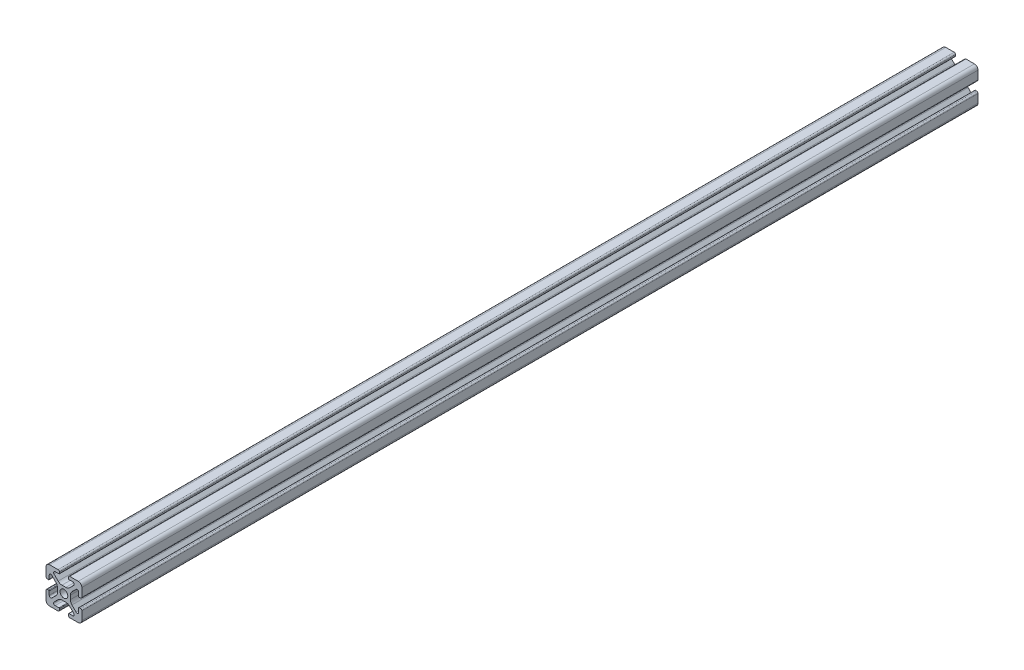
SolidWorks part; units mm, degrees
ref_plane "Front Plane" through (0, 0, 0) normal (0, 0, 1) x (1, 0, 0)
ref_plane "Top Plane" through (0, 0, 0) normal (0, 1, 0) x (1, 0, 0)
ref_plane "Right Plane" through (0, 0, 0) normal (1, 0, 0) x (0, 0, -1)
sketch "Sketch1" plane through (0, 0, 0) normal (0, 0, 1) x (1, 0, 0)
  line L0 (0, 10) -> (0, -10) construction
  line L1 (10, 0) -> (-10, 0) construction
  line L2 (-2.5, 10) -> (2.5, 10) construction
  line L3 (-5.75, 8.2) -> (5.75, 8.2) construction
  circle A0 centre (0, 0) radius 2.15 construction
  point P4 (0, 0)
  point P8 (0, 0)
  point P10 (0, 3.6)
  point P14 (0, 10)
  point P17 (0, 8.2)
  dimension "Thru Hole" = 4.3
  dimension "Height" = 20
  dimension "T Slot Depth" = 6.4
  dimension "T Slot Top Width" = 5
  dimension "T Slot Max Width" = 11.5
  dimension "Wall" = 1.8
sketch "Sketch2" plane through (0, 0, 0) normal (1, 0, 0) x (0, 0, -1)
  line L0 (250, 0) -> (-250, 0) construction
  point P4 (0, 0)
  dimension "D1" = 500
sketch "Sketch3" plane through (0, 0, 0) normal (0, 0, 1) x (1, 0, 0)
  line L0 (3.2874, 10) -> (8, 10)
  line L1 (10, 8) -> (10, -8) construction
  line L2 (8, -10) -> (-8, -10) construction
  line L3 (-10, 10) -> (10, -10) construction
  line L4 (2.5, 9.2126) -> (2.5, 8.5048)
  line L5 (-5.75, 8.2) -> (5.75, 8.2) construction
  line L6 (2.8048, 8.2) -> (4.9118, 8.2)
  line L7 (5.5045, 6.7691) -> (3.2141, 4.4787)
  line L8 (1.0928, 3.6) -> (-1.0928, 3.6)
  line L9 (0, 10) -> (0, -10) construction
  line L10 (5.75, 8.2) -> (5.75, 0) construction
  line L11 (10, 0) -> (-10, 0) construction
  line L12 (0, 0) -> (0, 10) construction
  line L13 (-2.5, 9.2126) -> (-2.5, 8.5048)
  line L14 (-5.5045, 6.7691) -> (-3.2141, 4.4787)
  line L15 (-2.8048, 8.2) -> (-4.9118, 8.2)
  line L16 (-3.2874, 10) -> (-8, 10)
  line L17 (0, 0) -> (-10, 0) construction
  line L18 (-10, 3.2874) -> (-10, 8)
  line L19 (-8.2, 2.8048) -> (-8.2, 4.9118)
  line L20 (-6.7691, 5.5045) -> (-4.4787, 3.2141)
  line L21 (-9.2126, 2.5) -> (-8.5048, 2.5)
  line L22 (-3.6, -1.0928) -> (-3.6, 1.0928)
  line L23 (-6.7691, -5.5045) -> (-4.4787, -3.2141)
  line L24 (-8.2, -2.8048) -> (-8.2, -4.9118)
  line L25 (-9.2126, -2.5) -> (-8.5048, -2.5)
  line L26 (-10, -3.2874) -> (-10, -8)
  line L27 (9.2126, -2.5) -> (8.5048, -2.5)
  line L28 (8.2, -2.8048) -> (8.2, -4.9118)
  line L29 (6.7691, -5.5045) -> (4.4787, -3.2141)
  line L30 (3.6, -1.0928) -> (3.6, 1.0928)
  line L31 (9.2126, 2.5) -> (8.5048, 2.5)
  line L32 (6.7691, 5.5045) -> (4.4787, 3.2141)
  line L33 (8.2, 2.8048) -> (8.2, 4.9118)
  line L34 (10, 8) -> (10, 3.2874)
  line L35 (10, -3.2874) -> (10, -8)
  line L36 (3.2874, -10) -> (8, -10)
  line L37 (-3.2874, -10) -> (-8, -10)
  line L38 (-6.7691, -5.5045) -> (-4.4787, -3.2141)
  line L39 (-2.8048, -8.2) -> (-4.9118, -8.2)
  line L40 (-5.5045, -6.7691) -> (-3.2141, -4.4787)
  line L41 (-2.5, -9.2126) -> (-2.5, -8.5048)
  line L42 (1.0928, -3.6) -> (-1.0928, -3.6)
  line L43 (5.5045, -6.7691) -> (3.2141, -4.4787)
  line L44 (2.8048, -8.2) -> (4.9118, -8.2)
  line L45 (2.5, -9.2126) -> (2.5, -8.5048)
  arc A0 (4.9118, 8.2) -> (5.5045, 6.7691) centre (4.9118, 7.3618) cw
  arc A1 (3.2141, 4.4787) -> (1.0928, 3.6) centre (1.0928, 6.6) cw
  circle A2 centre (0, 0) radius 2.15 construction
  circle A3 centre (0, 0) radius 2.15
  arc A4 (3.2874, 10) -> (2.5, 9.2126) centre (3.2874, 9.2126) ccw
  arc A5 (2.5, 8.5048) -> (2.8048, 8.2) centre (2.8048, 8.5048) ccw
  arc A6 (-3.2874, 10) -> (-2.5, 9.2126) centre (-3.2874, 9.2126) cw
  arc A7 (-4.9118, 8.2) -> (-5.5045, 6.7691) centre (-4.9118, 7.3618) ccw
  arc A8 (-3.2141, 4.4787) -> (-1.0928, 3.6) centre (-1.0928, 6.6) ccw
  arc A9 (-2.5, 8.5048) -> (-2.8048, 8.2) centre (-2.8048, 8.5048) cw
  arc A10 (-8.5048, 2.5) -> (-8.2, 2.8048) centre (-8.5048, 2.8048) ccw
  arc A11 (-4.4787, 3.2141) -> (-3.6, 1.0928) centre (-6.6, 1.0928) cw
  arc A12 (-8.2, 4.9118) -> (-6.7691, 5.5045) centre (-7.3618, 4.9118) cw
  arc A13 (-10, 3.2874) -> (-9.2126, 2.5) centre (-9.2126, 3.2874) ccw
  arc A14 (-8.5048, -2.5) -> (-8.2, -2.8048) centre (-8.5048, -2.8048) cw
  arc A15 (-10, -3.2874) -> (-9.2126, -2.5) centre (-9.2126, -3.2874) cw
  arc A16 (-4.4787, -3.2141) -> (-3.6, -1.0928) centre (-6.6, -1.0928) ccw
  arc A17 (-8.2, -4.9118) -> (-6.7691, -5.5045) centre (-7.3618, -4.9118) ccw
  arc A26 (-8, -10) -> (-10, -8) centre (-8, -8) cw
  arc A27 (-8, 10) -> (-10, 8) centre (-8, 8) ccw
  arc A28 (8, 10) -> (10, 8) centre (8, 8) cw
  arc A29 (10, -8) -> (8, -10) centre (8, -8) cw
  arc A30 (8.2, -4.9118) -> (6.7691, -5.5045) centre (7.3618, -4.9118) cw
  arc A31 (4.4787, -3.2141) -> (3.6, -1.0928) centre (6.6, -1.0928) cw
  arc A32 (10, -3.2874) -> (9.2126, -2.5) centre (9.2126, -3.2874) ccw
  arc A33 (8.5048, -2.5) -> (8.2, -2.8048) centre (8.5048, -2.8048) ccw
  arc A34 (10, 3.2874) -> (9.2126, 2.5) centre (9.2126, 3.2874) cw
  arc A35 (8.2, 4.9118) -> (6.7691, 5.5045) centre (7.3618, 4.9118) ccw
  arc A36 (4.4787, 3.2141) -> (3.6, 1.0928) centre (6.6, 1.0928) ccw
  arc A37 (8.5048, 2.5) -> (8.2, 2.8048) centre (8.5048, 2.8048) cw
  arc A38 (-2.5, -8.5048) -> (-2.8048, -8.2) centre (-2.8048, -8.5048) ccw
  arc A39 (-3.2141, -4.4787) -> (-1.0928, -3.6) centre (-1.0928, -6.6) cw
  arc A40 (-4.9118, -8.2) -> (-5.5045, -6.7691) centre (-4.9118, -7.3618) cw
  arc A41 (-3.2874, -10) -> (-2.5, -9.2126) centre (-3.2874, -9.2126) ccw
  arc A42 (2.5, -8.5048) -> (2.8048, -8.2) centre (2.8048, -8.5048) cw
  arc A43 (3.2874, -10) -> (2.5, -9.2126) centre (3.2874, -9.2126) cw
  arc A44 (3.2141, -4.4787) -> (1.0928, -3.6) centre (1.0928, -6.6) ccw
  arc A45 (4.9118, -8.2) -> (5.5045, -6.7691) centre (4.9118, -7.3618) ccw
  point P36 (2.5, 10)
  point P39 (2.5, 8.2)
  point P49 (0, 3.6)
  point P77 (-3.6, 0)
  point P78 (-8.2, -2.5)
  point P79 (-10, -2.5)
  point P104 (-10, -10)
  point P110 (10, 10)
  point P114 (10, -2.5)
  point P115 (8.2, -2.5)
  point P116 (3.6, 0)
  point P141 (0, -3.6)
  dimension "D1" = 3
  dimension "D2" = 0.8382
  dimension "D4" = 0.7874
  dimension "D5" = 0.3048
  dimension "D6" = 2
  dimension "D3" = 45
extrude "Boss-Extrude1" add sketch "Sketch3" along normal up to vertex (250 mm away) and the other way up to vertex (250 mm away) contours A45 L44 A42 L45 A43 L36 A29 L35 A32 L27 A33 L28 A30 L29 A31 L30 A36 L32 A35 L33 A37 L31 A34 L34 A28 L0 A4 L4 A5 L6 A0 L7 A1 L8 A8 L14 A7 L15 A9 L13 A6 L16 A27 L18 A13 L21 A10 L19 A12 L20 A11 up to point (0, 0, 250) other way up to point (0, 0, -250)
